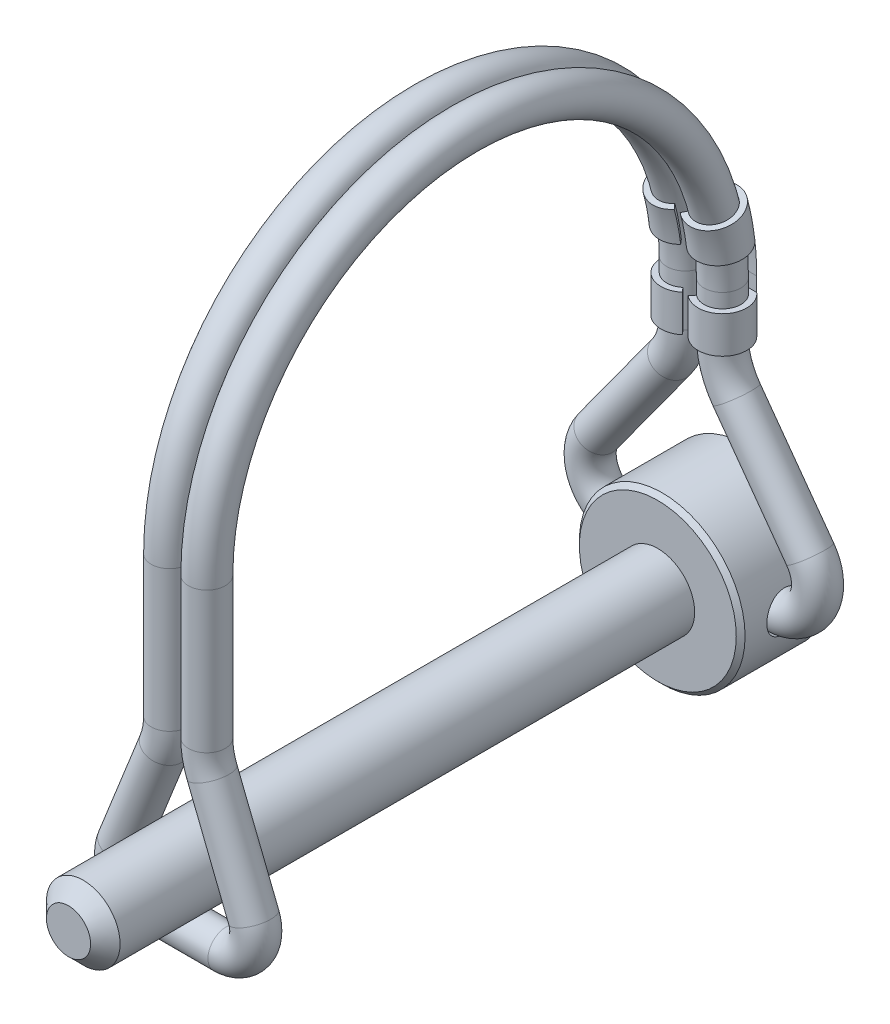
SolidWorks part; units mm, degrees
ref_plane "Front" through (0, 0, 0) normal (0, 0, 1) x (1, 0, 0)
ref_plane "Top" through (0, 0, 0) normal (0, 1, 0) x (1, 0, 0)
ref_plane "Right" through (0, 0, 0) normal (1, 0, 0) x (0, 0, -1)
sketch "Sketch1" plane through (0, 0, 0) normal (1, 0, 0) x (0, 0, -1)
  line L0 (-29.3687, 0) -> (29.3687, 0)
  line L1 (29.3687, 0) -> (29.3687, 6.7627)
  line L2 (28.9877, 7.1437) -> (21.8122, 7.1437)
  line L3 (21.4312, 6.7627) -> (21.4312, 3.175)
  line L4 (21.4312, 3.175) -> (-28.0987, 3.175)
  line L5 (-29.3687, 1.905) -> (-29.3687, 0)
  line L6 (0, 0) -> (0, 3.175) construction
  line L7 (0, 0) -> (0, -3.175) construction
  line L8 (25.4, 7.1437) -> (25.4, 0) construction
  line L9 (25.4, 0) -> (25.4, -7.1438) construction
  line L10 (-28.0987, 3.175) -> (-29.3687, 1.905)
  line L11 (21.8122, 7.1437) -> (21.4312, 6.7627)
  line L12 (29.3687, 6.7627) -> (28.9877, 7.1437)
  line L13 (-29.3687, 3.175) -> (-28.0987, 3.175) construction
  line L14 (-29.3687, 3.175) -> (-29.3687, 1.905) construction
  point P4 (29.3687, 7.1437)
  point P5 (21.4312, 7.1437)
  point P7 (-29.3687, 3.175)
  dimension "D1" = 6.35
  dimension "D2" = 14.2875
  dimension "D3" = 7.9375
  dimension "D4" = 50.8
  dimension "D5" = 1.27
revolve "Revolve1" add sketch "Sketch1" angle 360 mid plane about L0
sketch "Sketch2" plane through (0, 0, 0) normal (1, 0, 0) x (0, 0, -1)
  line L0 (21.4313, 0) -> (29.3688, 0) construction
  line L1 (21.4313, 3.175) -> (21.4313, -3.175) construction
  line L2 (29.3688, -6.7627) -> (29.3688, 6.7627) construction
  circle A0 centre (25.4, 0) radius 1.7145
  circle A1 centre (25.4, 0) radius 1.5875 construction
  dimension "D2" = 3.175
extrude "Cut-Extrude1" cut sketch "Sketch2" against normal through all and the other way through all
ref_plane "Plane1" through (1.6034, 0, 0) normal (1, 0, 0) x (0, 0, -1)
ref_plane "Plane2" through (-1.6034, 0, 0) normal (1, 0, 0) x (0, 0, -1)
sketch "Sketch3" plane through (1.6034, 0, 0) normal (1, 0, 0) x (0, 0, -1)
  line L0 (25.4, 0) -> (25.4, 18.4547) construction
  line L1 (25.4, 18.4547) -> (25.4, 22.225)
  line L3 (-19.05, 22.225) -> (-19.05, 10.7156)
  line L4 (25.4, -1.5875) -> (25.4, 1.5875) construction
  line L5 (25.4, 0) -> (-19.05, 0) construction
  line L6 (-19.05, 0) -> (-19.05, 10.7156) construction
  line L7 (3.175, 44.45) -> (3.175, 42.8625) construction
  line L8 (3.175, 42.8625) -> (3.175, 3.175) construction
  line L9 (21.4313, 3.175) -> (-28.0987, 3.175) construction
  line L10 (3.175, 44.45) -> (3.175, 46.0375) construction
  line L11 (-20.6375, 10.7156) -> (-17.4625, 10.7156) construction
  line L12 (23.8125, 18.4547) -> (26.9875, 18.4547) construction
  line L13 (-17.4625, 10.7156) -> (-17.4625, 22.225) construction
  line L14 (-17.4625, 22.225) -> (3.175, 22.225) construction
  arc A2 (25.4, 22.225) -> (-19.05, 22.225) centre (3.175, 22.225) ccw
  circle A3 centre (25.4, 0) radius 1.5875 construction
  dimension "D1" = 18.4547
  dimension "D3" = 10.7156
  dimension "D5" = 39.6875
  dimension "D4" = 3.175
  dimension "D2" = 20.6375
sketch "Sketch4" plane through (-1.6034, 0, 0) normal (1, 0, 0) x (0, 0, -1)
  line L3 (-19.05, 22.225) -> (-19.05, 10.7156) construction
  line L4 (25.4, 18.4547) -> (25.4, 22.225) construction
  line L6 (-19.05, 22.225) -> (-19.05, 10.7156)
  line L7 (25.4, 18.4547) -> (25.4, 22.225)
  arc A2 (25.4, 22.225) -> (-19.05, 22.225) centre (3.175, 22.225) ccw construction
  arc A3 (25.4, 22.225) -> (-19.05, 22.225) centre (3.175, 22.225) ccw
ref_plane "Plane3" through (0, 0, -25.4) normal (0, 0, -1) x (-1, 0, 0)
sketch "Sketch5" plane through (0, 0, -25.4) normal (0, 0, -1) x (-1, 0, 0)
  line L0 (-6.4294, 0) -> (6.4294, 0)
  line L1 (9.1591, 5.3578) -> (2.8163, 14.087)
  line L2 (0, 5.3578) -> (-9.1591, 5.3578) construction
  line L3 (-9.1591, 5.3578) -> (-2.8163, 14.087)
  line L4 (-1.6034, 0) -> (-1.6034, 18.4547) construction
  line L5 (-1.6034, 18.4547) -> (-1.6034, 17.8197)
  line L6 (1.6034, 18.4547) -> (1.6034, 17.8197)
  line L7 (0, 0) -> (0, 5.3578) construction
  arc A0 (-9.1591, 5.3578) -> (-6.4294, 0) centre (-6.4294, 3.3743) ccw
  arc A1 (6.4294, 0) -> (9.1591, 5.3578) centre (6.4294, 3.3743) ccw
  arc A2 (1.6034, 17.8197) -> (2.8163, 14.087) centre (7.9534, 17.8197) ccw
  arc A3 (-2.8163, 14.087) -> (-1.6034, 17.8197) centre (-7.9534, 17.8197) ccw
  point P20 (1.6034, 15.7563)
  point P23 (-1.6034, 15.7563)
  dimension "D2" = 6.35
  dimension "D3" = 0.635
  dimension "D1" = 12.8587
  dimension "D4" = 5.3578
ref_plane "Plane4" through (0, 0, 19.05) normal (0, 0, -1) x (-1, 0, 0)
sketch "Sketch6" plane through (0, 0, 19.05) normal (0, 0, -1) x (-1, 0, 0)
  line L0 (1.6034, 10.7156) -> (1.6034, 10.0806)
  line L1 (-1.6034, 10.7156) -> (-1.6034, 10.0806)
  line L2 (2.0541, 7.7311) -> (5.6466, -1.289)
  line L3 (3.2868, -4.7688) -> (-3.2868, -4.7688)
  line L4 (-5.6466, -1.289) -> (-2.0541, 7.7311)
  line L5 (0, -3.175) -> (0, -4.7688) construction
  line L6 (0, -4.7688) -> (0, -6.3627) construction
  line L7 (-4.4304, 1.7645) -> (-2.9497, 1.1748) construction
  line L8 (-4.4304, 1.7645) -> (-5.9111, 2.3543) construction
  arc A1 (-1.6034, 10.0806) -> (-2.0541, 7.7311) centre (-7.9534, 10.0806) cw
  arc A2 (1.6034, 10.0806) -> (2.0541, 7.7311) centre (7.9534, 10.0806) ccw
  circle A3 centre (0, 0) radius 3.175 construction
  circle A4 centre (0, 0) radius 3.175 construction
  arc A5 (-3.2868, -4.7688) -> (-5.6466, -1.289) centre (-3.2868, -2.2288) cw
  arc A6 (5.6466, -1.289) -> (3.2868, -4.7688) centre (3.2868, -2.2288) cw
  dimension "D1" = 6.35
  dimension "D4" = 2.54
  dimension "D2" = 0.635
  dimension "D3" = 3.1877
curve "CompCurve1"
sketch "Sketch7" plane through (0, 0, 0) normal (1, 0, 0) x (0, 0, -1)
  circle A0 centre (25.4, 0) radius 1.5875
  dimension "D1" = 3.175
sweep "Sweep1" add profiles "Sketch7" path "CompCurve1"
sketch "Sketch8" plane through (0, 0, 0) normal (1, 0, 0) x (0, 0, -1)
  line L0 (25.4, 18.4547) -> (25.4, 22.225) construction
  line L2 (25.4, 18.4547) -> (25.4, 22.225)
  line L3 (25.4, 18.4547) -> (25.4, 17.8197)
  line L4 (3.175, 22.225) -> (24.65, 27.9501) construction
  line L5 (26.9875, 17.8197) -> (23.8125, 17.8197) construction
  arc A0 (25.4, 22.225) -> (-19.05, 22.225) centre (3.175, 22.225) ccw construction
  arc A1 (25.4, 22.225) -> (24.65, 27.9501) centre (3.175, 22.225) ccw
  dimension "D1" = 9.525
ref_plane "Plane5" through (0, 17.8197, 0) normal (0, -1, 0) x (-1, 0, 0)
sketch "Sketch9" plane through (0, 17.8197, 0) normal (0, -1, 0) x (-1, 0, 0)
  line L0 (1.6034, 27.4955) -> (-1.6034, 27.4955)
  line L1 (0.254, 23.7968) -> (0.5811, 24.1854)
  line L2 (-0.254, 23.7968) -> (-0.5811, 24.1854)
  line L3 (1.6034, 26.9875) -> (-1.6034, 26.9875)
  line L4 (0, 27.4955) -> (0, 26.9875) construction
  line L5 (0.254, 23.7968) -> (-0.254, 23.7968) construction
  line L6 (1.6034, 25.4) -> (-1.6034, 25.4) construction
  arc A0 (0.5811, 24.1854) -> (1.6034, 26.9875) centre (1.6034, 25.4) ccw
  arc A1 (-1.6034, 26.9875) -> (-0.5811, 24.1854) centre (-1.6034, 25.4) ccw
  circle A2 centre (1.6034, 25.4) radius 1.5875 construction
  arc A3 (0.254, 23.7968) -> (1.6034, 27.4955) centre (1.6034, 25.4) ccw
  arc A4 (-1.6034, 27.4955) -> (-0.254, 23.7968) centre (-1.6034, 25.4) ccw
  dimension "D1" = 0.508
sweep "Sweep2" add profiles "Sketch9" path "Sketch8"
sketch "Sketch10" plane through (0, 0, 0) normal (1, 0, 0) x (0, 0, -1)
  line L0 (25.4, 17.8197) -> (26.9875, 17.8197) construction
  line L1 (26.9875, 17.8197) -> (23.8125, 17.8197) construction
  line L2 (23.8125, 17.8197) -> (26.9875, 17.8197) construction
  line L3 (26.9875, 20.9947) -> (26.9875, 22.225)
  line L4 (23.3045, 22.225) -> (27.4955, 22.225) construction
  line L5 (24.65, 27.9501) -> (26.1839, 28.359) construction
  line L6 (3.175, 22.225) -> (24.65, 27.9501) construction
  line L7 (26.9875, 20.9947) -> (3.175, 20.9947)
  line L8 (26.8242, 25.0091) -> (3.175, 22.225)
  line L9 (3.175, 22.225) -> (3.175, 20.9947)
  arc A0 (26.9875, 22.225) -> (26.8242, 25.0091) centre (3.175, 22.225) ccw
  dimension "D2" = 3.175
  dimension "D1" = 3.175
extrude "Cut-Extrude2" cut sketch "Sketch10" against normal through all both and the other way through all
equation "\"D5@Sketch1\"=\"D1@Sketch1\"*.2"
equation "\"D4@Sketch3\"=\"D2@Sketch2\""
equation "\"D1@Sketch3\"=(\"D5@Sketch3\"-\"D2@Sketch3\")*.96875"
equation "\"D3@Sketch3\"=(\"D5@Sketch3\"-\"D2@Sketch3\")*.5625"
equation "\"D1@Plane1\"=\"D2@Sketch2\"*.505"
equation "\"D1@Plane2\"= \"D1@Plane1\""
equation "\"D1@Sketch5\"=\"D2@Sketch1\"*.9"
equation "\"D4@Sketch5\"=\"D2@Sketch1\"*.375"
equation "\"D2@Sketch10\"=\"D1@Sketch10\""
